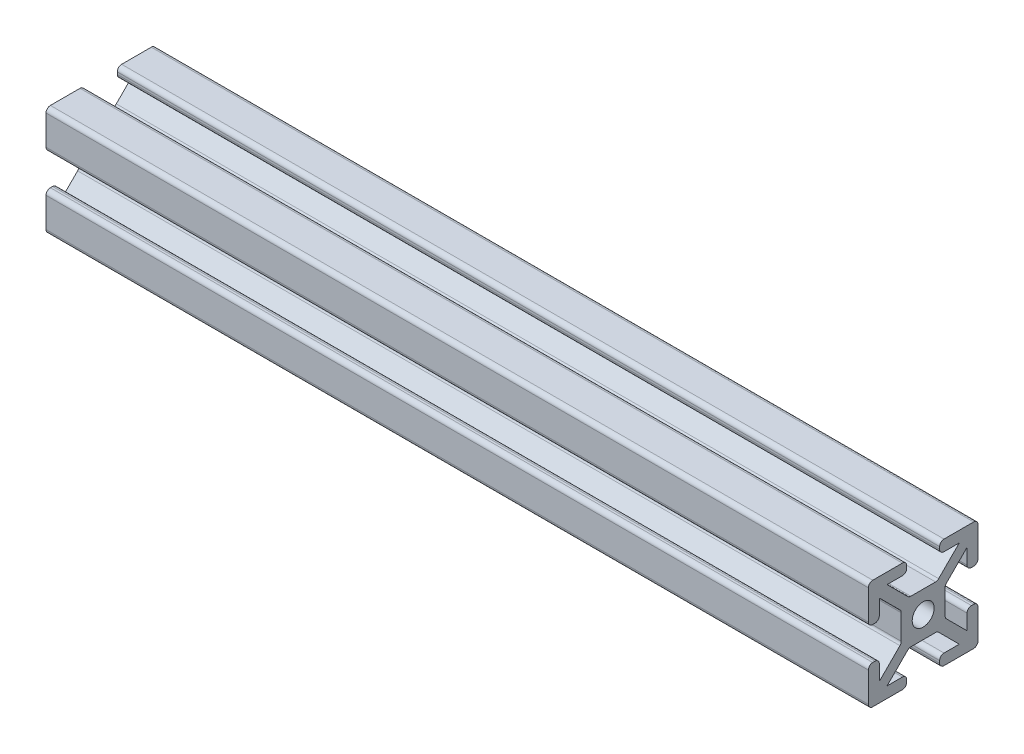
SolidWorks part; units mm, degrees
material "1060 Alloy"
ref_plane "Front Plane" through (0, 0, 0) normal (0, 0, 1) x (1, 0, 0)
ref_plane "Top Plane" through (0, 0, 0) normal (0, 1, 0) x (1, 0, 0)
ref_plane "Right Plane" through (0, 0, 0) normal (1, 0, 0) x (0, 0, -1)
sketch "Sketch2" plane through (0, 0, 0) normal (0, 0, 1) x (1, 0, 0)
  line L0 (-67.8105, 0) -> (82.1895, 0)
  dimension "D1" = 150
other "Profile 4X4(1)"
ref_plane "Plane1" through (-67.8105, 0, 0) normal (1, 0, 0) x (0, 1, 0)
sketch "Sketch1" plane through (-67.8105, 0, 0) normal (1, 0, 0) x (0, 1, 0)
  line L0 (-3, 9.2) -> (-3, 8.8)
  line L1 (-2.2544, 4) -> (2.2544, 4)
  line L2 (-4, 2.2544) -> (-4, -2.2544)
  line L3 (-2.2544, -4) -> (2.2544, -4)
  line L4 (4, 2.2544) -> (4, -2.2544)
  line L7 (-6.5858, 8) -> (-3.8, 8)
  line L8 (-8, 6.5858) -> (-8, 3.8)
  line L9 (-6.5858, -8) -> (-3.8, -8)
  line L10 (8, 6.5858) -> (8, 3.8)
  line L12 (9.7657, -9.7657) -> (10, -10) construction
  line L13 (-9.2, 10) -> (-3.8, 10)
  line L14 (-10, 9.2) -> (-10, 3.8)
  line L15 (-9.2, -10) -> (-3.8, -10)
  line L16 (10, 9.2) -> (10, 3.8)
  line L17 (-10, 10) -> (-9.7657, 9.7657) construction
  line L18 (-10, -10) -> (-9.7657, -9.7657) construction
  line L21 (3, 9.2) -> (3, 8.8)
  line L22 (3, -9.2) -> (3, -8.8)
  line L23 (-3, -9.2) -> (-3, -8.8)
  line L24 (3.8, 10) -> (9.2, 10)
  line L25 (3.8, 8) -> (6.5858, 8)
  line L26 (-9.2, 3) -> (-8.8, 3)
  line L27 (9.2, 3) -> (8.8, 3)
  line L28 (9.2, -3) -> (8.8, -3)
  line L29 (-9.2, -3) -> (-8.8, -3)
  line L30 (-10, -3.8) -> (-10, -9.2)
  line L31 (-8, -3.8) -> (-8, -6.5858)
  line L32 (8, -3.8) -> (8, -6.5858)
  line L33 (10, -3.8) -> (10, -9.2)
  line L34 (3.8, -8) -> (6.5858, -8)
  line L35 (3.8, -10) -> (9.2, -10)
  line L36 (6.5858, 8) -> (2.8201, 4.2343)
  line L37 (8, 6.5858) -> (4.2343, 2.8201)
  line L38 (8, -6.5858) -> (4.2343, -2.8201)
  line L39 (6.5858, -8) -> (2.8201, -4.2343)
  line L40 (-6.5858, -8) -> (-2.8201, -4.2343)
  line L41 (-8, -6.5858) -> (-4.2343, -2.8201)
  line L42 (-8, 6.5858) -> (-4.2343, 2.8201)
  line L43 (-6.5858, 8) -> (-2.8201, 4.2343)
  line L47 (9.7657, 9.7657) -> (10, 10) construction
  circle A0 centre (0, 0) radius 2
  arc A1 (9.2, -3) -> (10, -3.8) centre (9.2, -3.8) cw
  arc A2 (8.8, -3) -> (8, -3.8) centre (8.8, -3.8) ccw
  arc A3 (3, -9.2) -> (3.8, -10) centre (3.8, -9.2) ccw
  arc A4 (3, -8.8) -> (3.8, -8) centre (3.8, -8.8) cw
  arc A5 (-3, -9.2) -> (-3.8, -10) centre (-3.8, -9.2) cw
  arc A6 (-3, -8.8) -> (-3.8, -8) centre (-3.8, -8.8) ccw
  arc A7 (-8.8, -3) -> (-8, -3.8) centre (-8.8, -3.8) cw
  arc A8 (-9.2, -3) -> (-10, -3.8) centre (-9.2, -3.8) ccw
  arc A9 (-10, -9.2) -> (-9.2, -10) centre (-9.2, -9.2) ccw
  arc A10 (9.2, -10) -> (10, -9.2) centre (9.2, -9.2) ccw
  arc A11 (9.2, 10) -> (10, 9.2) centre (9.2, 9.2) cw
  arc A12 (-9.2, 10) -> (-10, 9.2) centre (-9.2, 9.2) ccw
  arc A13 (9.2, 3) -> (10, 3.8) centre (9.2, 3.8) ccw
  arc A14 (8.8, 3) -> (8, 3.8) centre (8.8, 3.8) cw
  arc A15 (3, 9.2) -> (3.8, 10) centre (3.8, 9.2) cw
  arc A16 (3, 8.8) -> (3.8, 8) centre (3.8, 8.8) ccw
  arc A17 (-3, 9.2) -> (-3.8, 10) centre (-3.8, 9.2) ccw
  arc A18 (-3, 8.8) -> (-3.8, 8) centre (-3.8, 8.8) cw
  arc A19 (-8.8, 3) -> (-8, 3.8) centre (-8.8, 3.8) ccw
  arc A20 (-9.2, 3) -> (-10, 3.8) centre (-9.2, 3.8) cw
  arc A21 (-2.8201, 4.2343) -> (-2.2544, 4) centre (-2.2544, 4.8) ccw
  arc A22 (4.2343, 2.8201) -> (4, 2.2544) centre (4.8, 2.2544) ccw
  arc A23 (2.8201, 4.2343) -> (2.2544, 4) centre (2.2544, 4.8) cw
  arc A24 (4.2343, -2.8201) -> (4, -2.2544) centre (4.8, -2.2544) cw
  arc A25 (2.8201, -4.2343) -> (2.2544, -4) centre (2.2544, -4.8) ccw
  arc A26 (-2.8201, -4.2343) -> (-2.2544, -4) centre (-2.2544, -4.8) cw
  arc A27 (-4.2343, -2.8201) -> (-4, -2.2544) centre (-4.8, -2.2544) ccw
  arc A28 (-4.2343, 2.8201) -> (-4, 2.2544) centre (-4.8, 2.2544) cw
  point P7 (0, 0)
  point P10 (-2.5858, 4)
  point P53 (10, -3)
  point P56 (8, -3)
  point P59 (3, -10)
  point P62 (3, -8)
  point P65 (-3, -10)
  point P68 (-3, -8)
  point P71 (-8, -3)
  point P74 (-10, -3)
  point P89 (10, 3)
  point P92 (8, 3)
  point P95 (3, 10)
  point P98 (3, 8)
  point P101 (-3, 10)
  point P104 (-3, 8)
  point P107 (-8, 3)
  point P110 (-10, 3)
  point P116 (4, 2.5858)
  point P119 (2.5858, 4)
  point P122 (4, -2.5858)
  point P125 (2.5858, -4)
  point P128 (-2.5858, -4)
  point P131 (-4, -2.5858)
  point P134 (-4, 2.5858)
  dimension "D3" = 4
  dimension "D11" = 0.8
  dimension "D12" = 0.8
  dimension "D2" = 0.8
  dimension "D4" = 20
  dimension "D6" = 20
  dimension "D8" = 7
  dimension "D9" = 7
